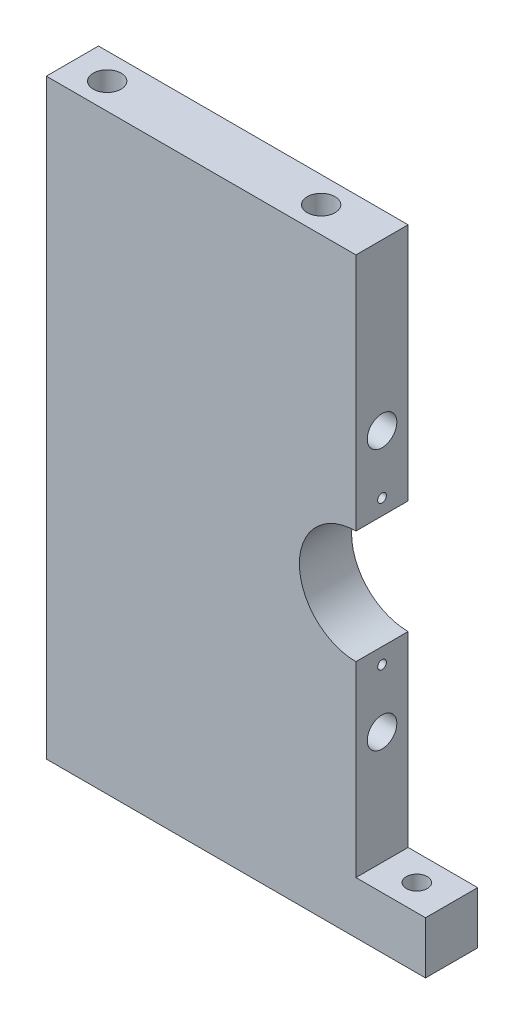
SolidWorks part; units mm, degrees
ref_plane "Front Plane" through (0, 0, 0) normal (0, 0, 1) x (1, 0, 0)
ref_plane "Top Plane" through (0, 0, 0) normal (0, 1, 0) x (1, 0, 0)
ref_plane "Right Plane" through (0, 0, 0) normal (1, 0, 0) x (0, 0, -1)
sketch "Sketch1" plane through (0, 0, 0) normal (0, 0, 1) x (1, 0, 0)
  line L0 (0, 0) -> (0, 340)
  line L1 (0, 340) -> (178, 340)
  line L2 (178, 340) -> (178, 202.5)
  line L3 (178, 137.5) -> (178, 30)
  line L4 (178, 30) -> (218, 30)
  line L5 (218, 30) -> (218, 0)
  line L6 (218, 0) -> (0, 0)
  arc A0 (178, 202.5) -> (178, 137.5) centre (178, 170) ccw
  dimension "D2" = 32.5
  dimension "D6" = 170
  dimension "D1" = 340
  dimension "D3" = 30
  dimension "D4" = 218
  dimension "D5" = 178
extrude "Boss-Extrude1" add sketch "Sketch1" along normal blind 30
sketch "Sketch2" plane through (178, 0, 0) normal (1, 0, 0) x (0, 0, -1)
  line L1 (-30, 30) -> (-30, 137.5) construction
  line L2 (-30, 0) -> (0, 0) construction
  circle A0 centre (-15, 95) radius 8.5
  dimension "D1" = 95
  dimension "D2" = 17
  dimension "D3" = 15
extrude "Cut-Extrude1" cut sketch "Sketch2" against normal through all
pattern_linear "LPattern1" count 2 spacing 150 along (0, 1, 0) of "Cut-Extrude1"
sketch "Sketch3" plane through (178, 0, 0) normal (1, 0, 0) x (0, 0, -1)
  line L0 (-30, 30) -> (-30, 137.5) construction
  circle A0 centre (-15, 128.5) radius 2.5
  circle A3 centre (-15, 95) radius 8.5 construction
  dimension "D1" = 5
  dimension "D2" = 33.5
  dimension "D3" = 15
extrude "Cut-Extrude2" cut sketch "Sketch3" against normal blind 15
pattern_linear "LPattern2" count 2 spacing 83 along (0, 1, 0) of "Cut-Extrude2"
sketch "Sketch4" plane through (0, 30, 0) normal (0, 1, 0) x (1, 0, 0)
  line L0 (218, -30) -> (218, 0) construction
  line L1 (218, -30) -> (178, -30) construction
  circle A0 centre (198, -15) radius 6
  dimension "D1" = 12
  dimension "D3" = 15
  dimension "D2" = 20
extrude "Cut-Extrude3" cut sketch "Sketch4" against normal through all
sketch "Sketch5" plane through (0, 340, 0) normal (0, 1, 0) x (1, 0, 0)
  line L0 (178, -30) -> (0, -30) construction
  line L1 (0, -30) -> (0, 0) construction
  circle A0 centre (20, -15) radius 8
  circle A1 centre (143, -15) radius 8
  dimension "D1" = 15
  dimension "D2" = 16
  dimension "D3" = 123
  dimension "D4" = 20
extrude "Cut-Extrude4" cut sketch "Sketch5" against normal blind 40
